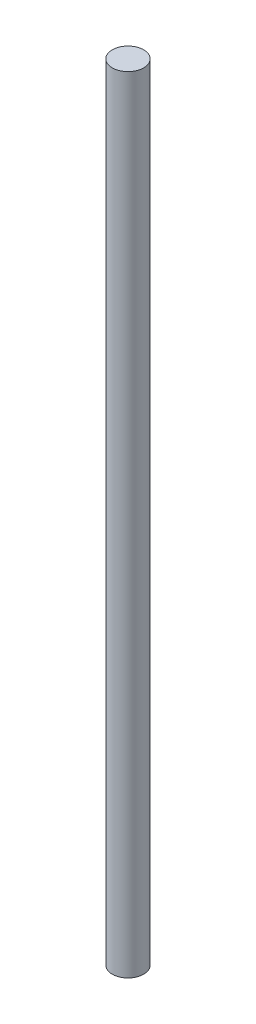
SolidWorks part; units mm, degrees
ref_plane "Front Plane" through (0, 0, 0) normal (0, 0, 1) x (1, 0, 0)
ref_plane "Top Plane" through (0, 0, 0) normal (0, 1, 0) x (1, 0, 0)
ref_plane "Right Plane" through (0, 0, 0) normal (1, 0, 0) x (0, 0, -1)
sketch "Sketch1" plane through (0, 0, 0) normal (0, 1, 0) x (1, 0, 0)
  circle A0 centre (0, 0) radius 4
  point P4 (0, 0)
extrude "Boss-Extrude1" add sketch "Sketch1" along normal blind 200
hole_wizard "M4x0.7 Tapped Hole1" positions "Sketch2" profile "Sketch4" tap size "M4x0.7" standard "ANSI Metric"
sketch "Sketch2" plane through (0, 0, 0) normal (0, -1, 0) x (-1, 0, 0)
  point P0 (0, 0)
sketch "Sketch4" plane through (0, 0, 0) normal (1, 0, 0) x (0, 0, -1)
  line L0 (0, 0) -> (0, 10.0914)
  line L1 (0, 10.0914) -> (1.65, 9.1)
  line L2 (1.65, 9.1) -> (1.65, 0)
  line L5 (1.65, 0) -> (0, 0)
  line L10 (0, 10.0914) -> (-1.65, 9.1) construction
  line L11 (0, -6.35) -> (0, 107.95) construction
  dimension "Tap Drill Dia." = 3.3
  dimension "Tap Drill Depth" = 9.1
  dimension "Drill Angle" = 118
